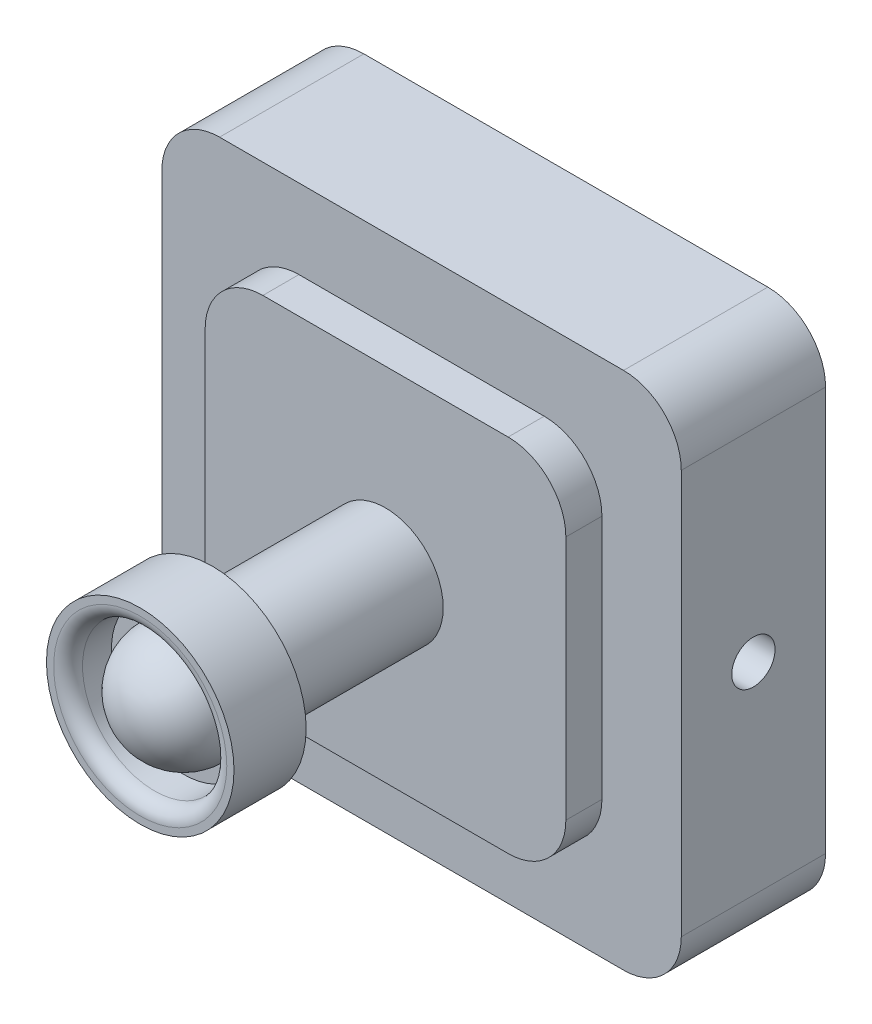
SolidWorks part; units mm, degrees
material "Ductile Iron (SN)"
ref_plane "前视基准面" through (0, 0, 0) normal (0, 0, 1) x (1, 0, 0)
ref_plane "上视基准面" through (0, 0, 0) normal (0, 1, 0) x (1, 0, 0)
ref_plane "右视基准面" through (0, 0, 0) normal (1, 0, 0) x (0, 0, -1)
other "Configuration Table"
sketch "Sketch1" plane through (0, 0, 0) normal (0, 0, 1) x (1, 0, 0)
  line L1 (0, 0) -> (36, 0)
  line L2 (0, 0) -> (0, 36)
  line L3 (0, 36) -> (36, 36)
  line L4 (36, 0) -> (36, 36)
  dimension "D1" = 36
  dimension "D2" = 36
extrude "Boss-Extrude1" add sketch "Sketch1" along normal blind 10
sketch "Sketch2" plane through (0, 0, 10) normal (0, 0, 1) x (1, 0, 0)
  line L0 (36, 36) -> (0, 36) construction
  line L1 (5.5, 30.5) -> (30.5, 30.5)
  line L2 (5.5, 30.5) -> (5.5, 5.5)
  line L3 (5.5, 5.5) -> (30.5, 5.5)
  line L4 (30.5, 30.5) -> (30.5, 5.5)
  line L5 (5.5, 30.5) -> (30.5, 5.5) construction
  line L6 (5.5, 5.5) -> (30.5, 30.5) construction
  line L7 (0, 36) -> (0, 0) construction
  point P0 (18, 18)
  dimension "D1" = 25
  dimension "D2" = 25
  dimension "D3" = 5.5
  dimension "D4" = 5.5
extrude "Boss-Extrude2" add sketch "Sketch2" along normal blind 2.5
sketch "Sketch3" plane through (0, 0, 12.5) normal (0, 0, 1) x (1, 0, 0)
  line L0 (30.5, 5.5) -> (30.5, 30.5) construction
  line L1 (5.5, 5.5) -> (30.5, 5.5) construction
  circle A0 centre (18, 18) radius 4
  dimension "D1" = 8
  dimension "D2" = 12.5
  dimension "D3" = 12.5
extrude "Boss-Extrude3" add sketch "Sketch3" along normal blind 12
sketch "Sketch4" plane through (0, 0, 24.5) normal (0, 0, 1) x (1, 0, 0)
  circle A0 centre (18, 18) radius 6.5
  dimension "D1" = 13
extrude "Boss-Extrude4" add sketch "Sketch4" along normal blind 5
sketch "Sketch5" plane through (0, 0, 29.5) normal (0, 0, 1) x (1, 0, 0)
  circle A0 centre (18, 18) radius 5
  dimension "D1" = 10
extrude "Cut-Extrude1" cut sketch "Sketch5" against normal blind 3
sketch "Sketch6" plane through (0, 0, 26.5) normal (0, 0, 1) x (1, 0, 0)
  line L0 (18, 18) -> (18, 16.6978) construction
  line L1 (18, 22) -> (18, 14)
  line L2 (18, 14) -> (18, 13.1889) construction
  arc A0 (18, 14) -> (18, 22) centre (18, 18) ccw
  dimension "D1" = 8
revolve "Revolve4" add sketch "Sketch6" angle 360 about L1
fillet "Fillet1" radius 4 4 edges at (5.5, 30.5, 11.25) (30.5, 30.5, 11.25) (5.5, 5.5, 11.25) (30.5, 5.5, 11.25)
fillet "Fillet2" radius 4 4 edges at (0, 36, 5) (36, 36, 5) (36, 0, 5) (0, 0, 5)
sketch "Sketch7" plane through (36, 0, 0) normal (1, 0, 0) x (0, 0, -1)
  line L0 (-10, 36) -> (0, 36) construction
  line L2 (0, 4) -> (0, 32) construction
  circle A0 centre (-5, 18) radius 1.5
  point P6 (0, 20.5113)
  dimension "D1" = 3
  dimension "D2" = 18
  dimension "D3" = 5
extrude "Cut-Extrude2" cut sketch "Sketch7" against normal blind 5
sketch "Sketch8" plane through (0, 0, 0) normal (-1, 0, 0) x (0, 0, 1)
  circle A1 centre (5, 18) radius 1.5
  circle A2 centre (5, 18) radius 1.5
  dimension "D1" = 0
extrude "Cut-Extrude3" cut sketch "Sketch8" against normal blind 5 contours A2
fillet "Fillet3" radius 1 1 edges at (23, 18, 29.5)
